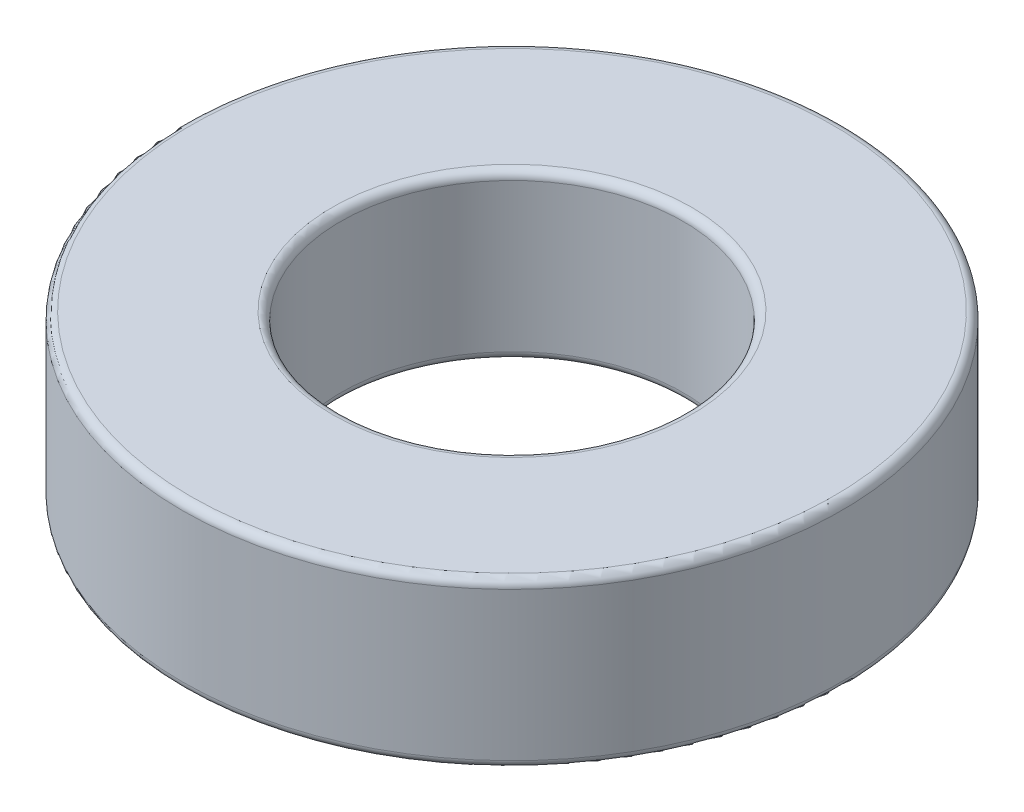
SolidWorks part; units mm, degrees
ref_plane "Front Plane" through (0, 0, 0) normal (0, 0, 1) x (1, 0, 0)
ref_plane "Top Plane" through (0, 0, 0) normal (0, 1, 0) x (1, 0, 0)
ref_plane "Right Plane" through (0, 0, 0) normal (1, 0, 0) x (0, 0, -1)
sketch "Sketch2" plane through (0, 0, 0) normal (0, 1, 0) x (1, 0, 0)
  circle A0 centre (0, 0) radius 3.302
  circle A1 centre (0, 0) radius 6.35
  dimension "OD" = 12.7
  dimension "ID" = 6.604
extrude "Spacer" add sketch "Sketch2" along normal blind 3.175
fillet "Fillet" radius 0.1588 4 edges at (0, 0, 3.302) (0, 0, 6.35) (0, 3.175, 3.302) (0, 3.175, 6.35)
equation "\"OD@Sketch2\"=.5"
equation "\"ID@Sketch2\" = .26in"
equation "\"D1@Spacer\" = .125"
equation "\"D1@Fillet\" = \"D1@Spacer\" / 20"
